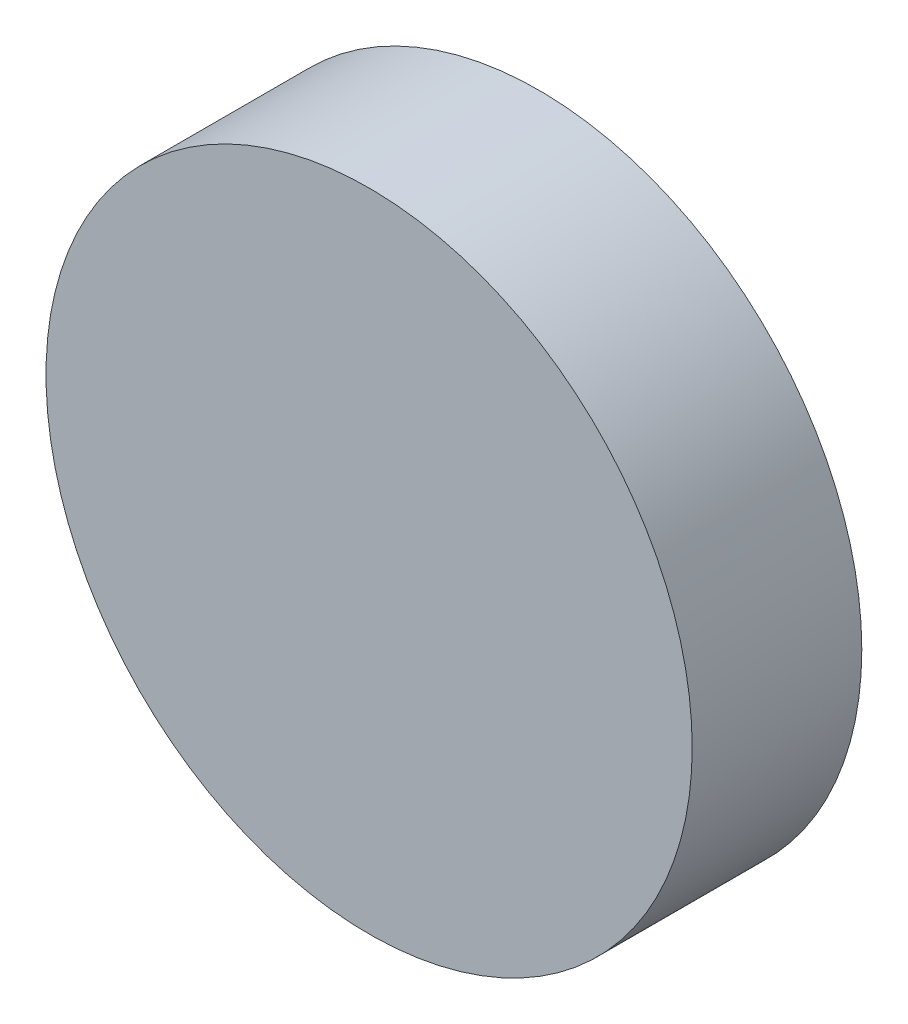
SolidWorks part; units mm, degrees
ref_plane "前视基准面" through (0, 0, 0) normal (0, 0, 1) x (1, 0, 0)
ref_plane "上视基准面" through (0, 0, 0) normal (0, 1, 0) x (1, 0, 0)
ref_plane "右视基准面" through (0, 0, 0) normal (1, 0, 0) x (0, 0, -1)
sketch "草图1" plane through (0, 0, 0) normal (0, 0, 1) x (1, 0, 0)
  circle A0 centre (0, 0) radius 19.05
  dimension "D1" = 38.1
extrude "凸台-拉伸1" add sketch "草图1" along normal blind 10 contours A0
